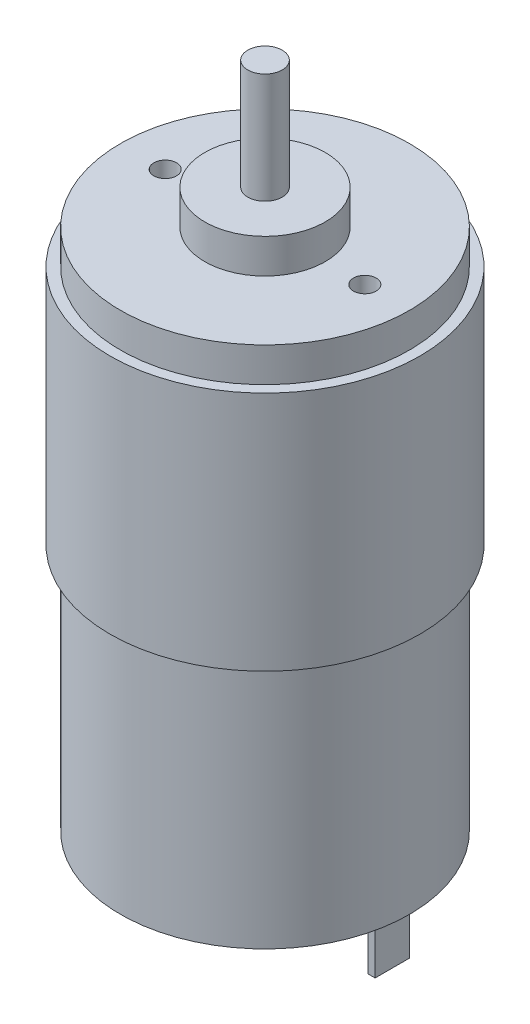
SolidWorks part; units mm, degrees
ref_plane "Front Plane" through (0, 0, 0) normal (0, 0, 1) x (1, 0, 0)
ref_plane "Top Plane" through (0, 0, 0) normal (0, 1, 0) x (1, 0, 0)
ref_plane "Right Plane" through (0, 0, 0) normal (1, 0, 0) x (0, 0, -1)
sketch "Sketch1" plane through (0, 0, 0) normal (0, 0, 1) x (1, 0, 0)
  line L0 (0, 0) -> (0, 105)
  line L1 (0, 105) -> (2.5, 105)
  line L2 (2.5, 105) -> (2.5, 89)
  line L3 (2.5, 89) -> (8.75, 89)
  line L4 (8.75, 89) -> (8.75, 84)
  line L5 (8.75, 84) -> (21, 84)
  line L6 (21, 84) -> (21, 79)
  line L7 (21, 79) -> (22.5, 79)
  line L8 (22.5, 79) -> (22.5, 44)
  line L9 (22.5, 44) -> (21, 44)
  line L10 (21, 44) -> (21, 8)
  line L11 (21, 8) -> (8.75, 8)
  line L12 (8.75, 8) -> (8.75, 3)
  line L13 (8.75, 3) -> (2.5, 3)
  line L14 (2.5, 3) -> (2.5, 0)
  line L15 (2.5, 0) -> (0, 0)
  point P3 (2.9015, 4.4262)
  point P18 (22.5, 79.2455)
  dimension "D1" = 5
  dimension "D2" = 16
  dimension "D3" = 2.5
  dimension "D4" = 8.75
  dimension "D5" = 21
  dimension "D6" = 22.5
  dimension "D7" = 76
  dimension "D8" = 105
  dimension "D9" = 5
  dimension "D10" = 35
revolve "Revolve1" add sketch "Sketch1" angle 360 about L0
sketch "Sketch2" plane through (0, 84, 0) normal (0, 1, 0) x (1, 0, 0)
  line L0 (0, 0) -> (0, 22.5) construction
  line L1 (14.5, 0) -> (0, 0) construction
  circle A0 centre (0, 0) radius 22.5 construction
  circle A1 centre (14.5, 0) radius 1.65
  circle A2 centre (-14.5, 0) radius 1.65
  dimension "D1" = 3.3
  dimension "D2" = 29
extrude "Cut-Extrude1" cut sketch "Sketch2" against normal blind 20
sketch "Sketch3" plane through (0, 8, 0) normal (0, -1, 0) x (1, 0, 0)
  line L0 (-22.5, 0) -> (22.5, 0) construction
  line L1 (0, -22.5) -> (0, 22.5) construction
  line L2 (-18.5, -2.5) -> (-17.5, -2.5)
  line L3 (-18.5, -2.5) -> (-18.5, 2.5)
  line L4 (-18.5, 2.5) -> (-17.5, 2.5)
  line L5 (-17.5, -2.5) -> (-17.5, 2.5)
  line L6 (-18.5, -2.5) -> (-17.5, 2.5) construction
  line L7 (-18.5, 2.5) -> (-17.5, -2.5) construction
  line L8 (18.5, 2.5) -> (17.5, 2.5)
  line L9 (17.5, -2.5) -> (17.5, 2.5)
  line L10 (18.5, -2.5) -> (17.5, -2.5)
  line L11 (18.5, -2.5) -> (18.5, 2.5)
  circle A0 centre (0, 0) radius 22.5 construction
  point P5 (-18, 0)
  dimension "D1" = 35
  dimension "D2" = 1
  dimension "D3" = 5
extrude "Boss-Extrude1" add sketch "Sketch3" along normal up to surface (8 mm away) up to face at (0, 0, -2.5)
